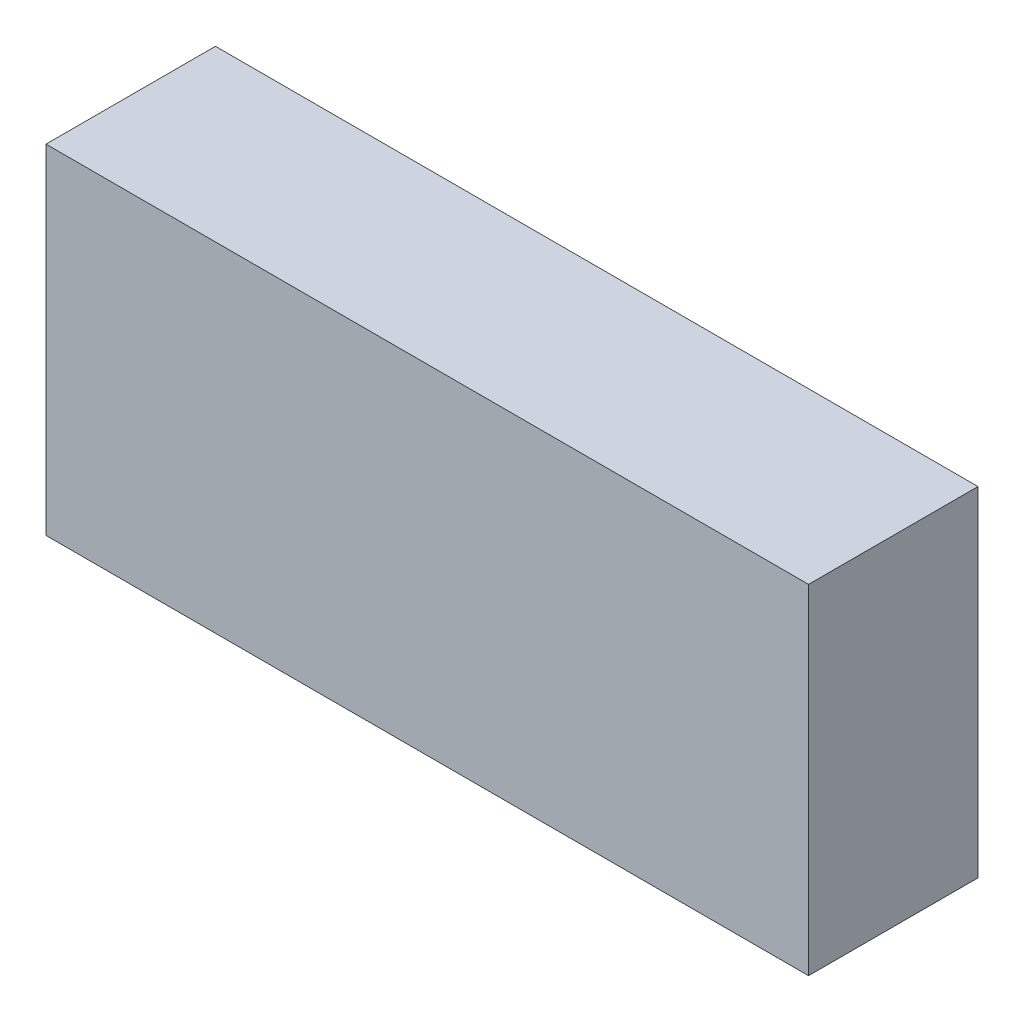
SolidWorks part; units mm, degrees
ref_plane "Front Plane" through (0, 0, 0) normal (0, 0, 1) x (1, 0, 0)
ref_plane "Top Plane" through (0, 0, 0) normal (0, 1, 0) x (1, 0, 0)
ref_plane "Right Plane" through (0, 0, 0) normal (1, 0, 0) x (0, 0, -1)
sketch "Sketch1" plane through (0, 0, 0) normal (0, 0, 1) x (1, 0, 0)
  line L1 (0, 0) -> (114.3, 0)
  line L2 (0, 0) -> (0, 50.8)
  line L3 (0, 50.8) -> (114.3, 50.8)
  line L4 (114.3, 0) -> (114.3, 50.8)
  dimension "D1" = 114.3
  dimension "D2" = 50.8
extrude "Boss-Extrude1" add sketch "Sketch1" along normal blind 25.4
